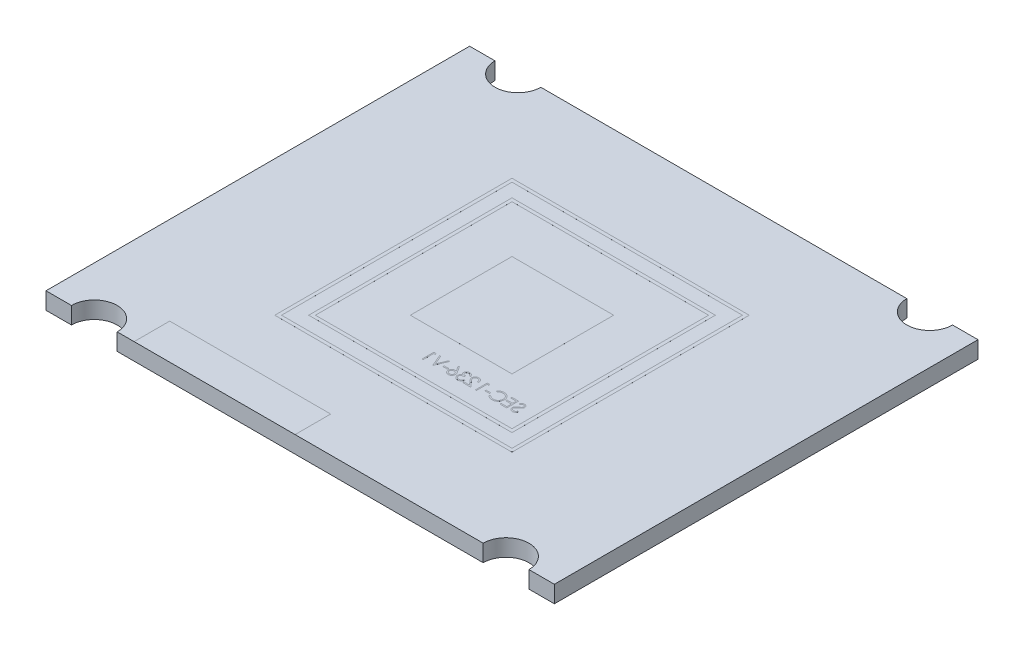
SolidWorks part; units mm, degrees
ref_plane "Plano frontal" through (0, 0, 0) normal (0, 0, 1) x (1, 0, 0)
ref_plane "Plano superior" through (0, 0, 0) normal (0, 1, 0) x (1, 0, 0)
ref_plane "Plano direito" through (0, 0, 0) normal (1, 0, 0) x (0, 0, -1)
sketch "Sketch1" plane through (0, 0, 0) normal (0, 1, 0) x (1, 0, 0)
  line L1 (-15, 12.5) -> (15, 12.5)
  line L2 (-15, 12.5) -> (-15, -12.5)
  line L3 (-15, -12.5) -> (15, -12.5)
  line L4 (15, 12.5) -> (15, -12.5)
  point P4 (0, 12.5)
  point P6 (-15, 0)
  dimension "D1" = 30
  dimension "D2" = 25
extrude "Boss-Extrude1" add sketch "Sketch1" along normal mid plane 1
sketch "Sketch2" plane through (0, 0, 0) normal (0, 1, 0) x (1, 0, 0)
  line L1 (-3, 3) -> (3, 3)
  line L2 (-3, 3) -> (-3, -3)
  line L3 (-3, -3) -> (3, -3)
  line L4 (3, 3) -> (3, -3)
  point P4 (0, 3)
  point P6 (-3, 0)
  dimension "D1" = 6
  dimension "D2" = 6
sketch "Sketch3" plane through (0, 0, 0) normal (0, 1, 0) x (1, 0, 0)
  line L0 (15, 12.5) -> (-15, 12.5) construction
  line L4 (-15, 12.5) -> (-15, -12.5) construction
  line L5 (0, -1.7053) -> (0, 1.7053) construction
  line L6 (-1.7053, 0) -> (1.7053, 0) construction
  circle A0 centre (-12.15, 12.5) radius 1.35
  circle A1 centre (12.15, 12.5) radius 1.35
  circle A2 centre (12.15, -12.5) radius 1.35
  circle A3 centre (-12.15, -12.5) radius 1.35
  dimension "D1" = 2.7
  dimension "D2" = 1.5
extrude "Cut-Extrude2" cut sketch "Sketch3" against normal through all both and the other way through all
extrude "Boss-Extrude2" add sketch "Sketch2" along normal mid plane 1.0001
sketch "Sketch4" plane through (0, -0.5, 0) normal (0, -1, 0) x (1, 0, 0)
  circle A0 centre (0, 0) radius 2.25
  dimension "D1" = 4.5
extrude "Boss-Extrude3" add sketch "Sketch4" along normal blind 2
sketch "Sketch5" plane through (0, -2.5001, 0) normal (0, -1, 0) x (1, 0, 0)
  circle A0 centre (0, 0) radius 0.5
  dimension "D1" = 1
extrude "Cut-Extrude3" cut sketch "Sketch5" against normal blind 0.4
sketch "Sketch6" plane through (0, -2.1, 0) normal (0, -1, 0) x (1, 0, 0)
  line L0 (-0.5, 0) -> (0.5, 0)
  circle A0 centre (0, 0) radius 0.5 construction
  circle A1 centre (0, 0) radius 0.5 construction
  arc A2 (0.5, 0) -> (-0.5, 0) centre (0, 0) ccw
revolve "Revolve1" add sketch "Sketch6" angle 180 about L0
chamfer "Chamfer1" distance 0.2 angle 45 3 edges at (0, -2.5001, -2.25) (0, -2.5001, -0.5) (0, -0.5, -2.25)
sketch "Sketch9" plane through (0, 0, 0) normal (0, 1, 0) x (1, 0, 0)
  line L0 (-10.8, -12.5) -> (10.8, -12.5) construction
  line L1 (-9.8, -10.4) -> (-0.3, -10.4)
  line L2 (-9.8, -10.4) -> (-9.8, -12.5)
  line L3 (-9.8, -12.5) -> (-0.3, -12.5)
  line L4 (-0.3, -10.4) -> (-0.3, -12.5)
  dimension "D1" = 9.5
  dimension "D2" = 1
  dimension "D3" = 2.1
extrude "Marcação Fios" add sketch "Sketch9" along normal mid plane 1.0001
sketch "Sketch10" plane through (0, 0, 0) normal (0, 1, 0) x (1, 0, 0)
  line L0 (-6, -6) -> (6, -6)
  line L1 (-5.8, -5.8) -> (5.8, -5.8)
  line L2 (-5.8, -5.8) -> (-5.8, 5.8)
  line L3 (-5.8, 5.8) -> (5.8, 5.8)
  line L4 (5.8, -5.8) -> (5.8, 5.8)
  line L5 (6, -6) -> (6, 6)
  line L6 (-6, 6) -> (6, 6)
  line L7 (-6, -6) -> (-6, 6)
  line L8 (6.8, 6.8) -> (-6.8, 6.8)
  line L9 (7, 7) -> (-7, 7)
  line L10 (7, 7) -> (7, -7)
  line L11 (7, -7) -> (-7, -7)
  line L12 (-7, 7) -> (-7, -7)
  line L13 (-6.8, 6.8) -> (-6.8, -6.8)
  line L14 (6.8, -6.8) -> (-6.8, -6.8)
  line L15 (6.8, 6.8) -> (6.8, -6.8)
  point P0 (0, 0)
  point P6 (0, 5.8)
  point P7 (5.8, 0)
  point P16 (0, -7)
  point P17 (7, 0)
  dimension "D1" = 12
  dimension "D2" = 12
  dimension "D4" = 14
  dimension "D5" = 14
extrude "Contorno Câmera" add sketch "Sketch10" along normal mid plane 1.001 contours L9 L12 L11 L10 L8 L15 L14 L13 | L7 L0 L5 L6 L4 L1 L2 L3
sketch "Sketch11" plane through (0, 0, 0) normal (0, 1, 0) x (1, 0, 0)
  text T0 "SEC-1236-V1" font "Century Gothic" height 0.7
extrude "Boss-Extrude6" add sketch "Sketch11" along normal mid plane 1.001
